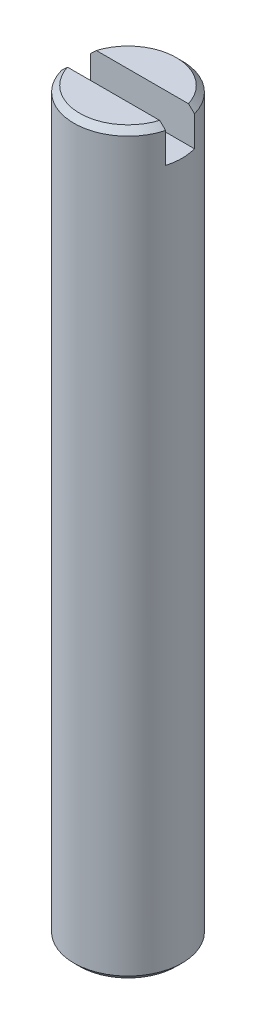
SolidWorks part; units mm, degrees
ref_plane "Front Plane" through (0, 0, 0) normal (0, 0, 1) x (1, 0, 0)
ref_plane "Top Plane" through (0, 0, 0) normal (0, 1, 0) x (1, 0, 0)
ref_plane "Right Plane" through (0, 0, 0) normal (1, 0, 0) x (0, 0, -1)
sketch "Sketch1" plane through (0, 0, 0) normal (0, 1, 0) x (1, 0, 0)
  circle A0 centre (0, 0) radius 1.875
  dimension "D1" = 3.75
extrude "Boss-Extrude1" add sketch "Sketch1" along normal blind 25.63
chamfer "Chamfer1" distance 0.2 angle 45 1 edges at (0, 25.63, 1.875)
chamfer "Chamfer2" distance 0.2 angle 45 1 edges at (0, 0, 1.875)
sketch "Sketch2" plane through (0, 25.63, 0) normal (0, 1, 0) x (1, 0, 0)
  line L1 (-1.9282, -0.5) -> (1.9282, -0.5)
  line L2 (-1.9282, -0.5) -> (-1.9282, 0.5)
  line L3 (-1.9282, 0.5) -> (1.9282, 0.5)
  line L4 (1.9282, -0.5) -> (1.9282, 0.5)
  line L5 (-1.9282, -0.5) -> (1.9282, 0.5) construction
  line L6 (-1.9282, 0.5) -> (1.9282, -0.5) construction
  point P0 (0, 0)
  dimension "D1" = 1
extrude "Cut-Extrude1" cut sketch "Sketch2" against normal blind 1.25
